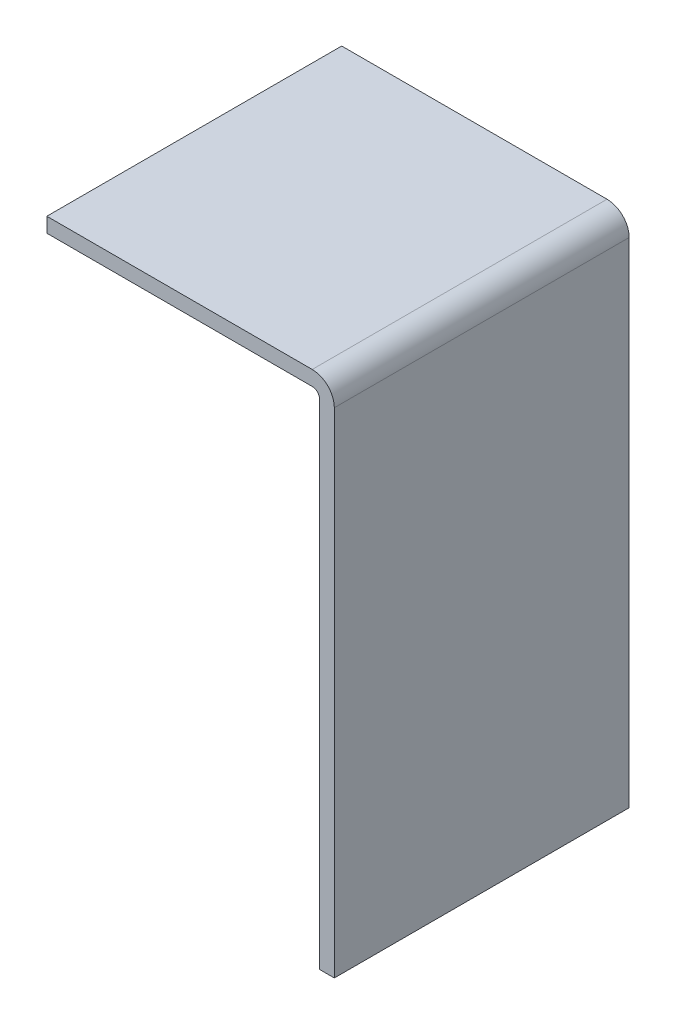
SolidWorks part; units mm, degrees
ref_plane "Plan de face" through (0, 0, 0) normal (0, 0, 1) x (1, 0, 0)
ref_plane "Plan de dessus" through (0, 0, 0) normal (0, 1, 0) x (1, 0, 0)
ref_plane "Plan de droite" through (0, 0, 0) normal (1, 0, 0) x (0, 0, -1)
sketch "Esquisse1" plane through (0, 0, 0) normal (0, 0, 1) x (1, 0, 0)
  line L0 (-3, 0) -> (-39, 0)
  line L1 (0, -3) -> (0, -70)
  line L2 (-3, -2) -> (-39, -2)
  line L3 (-2, -3) -> (-2, -70)
  line L4 (-2, -2) -> (-39, -2) construction
  line L5 (-2, -2) -> (-2, -70) construction
  line L6 (0, 0) -> (0, -70) construction
  line L7 (0, 0) -> (-39, 0) construction
  line L8 (-39, 0) -> (-39, -2)
  line L9 (-2, -70) -> (0, -70)
  arc A0 (-3, -2) -> (-2, -3) centre (-3, -3) cw
  arc A1 (0, -3) -> (-3, 0) centre (-3, -3) ccw
  point P13 (0, 0)
  dimension "D2" = 1
  dimension "D3" = 3
  dimension "D1" = 2
extrude "Extrusion1" add sketch "Esquisse1" along normal blind 40
